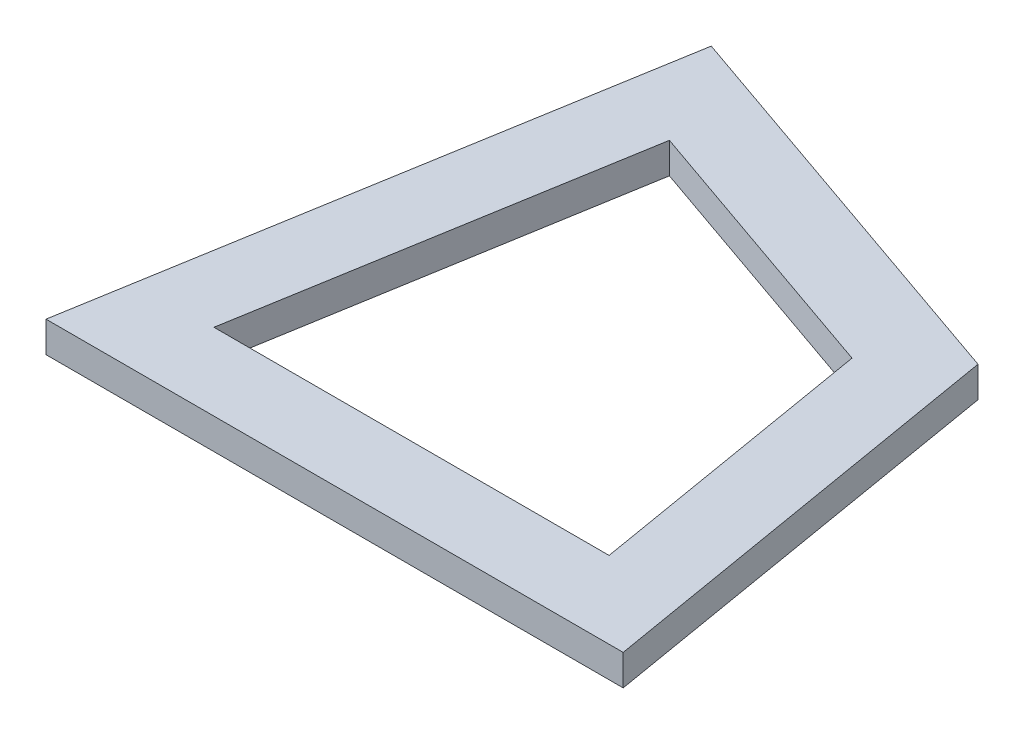
SolidWorks part; units mm, degrees
ref_plane "Front Plane" through (0, 0, 0) normal (0, 0, 1) x (1, 0, 0)
ref_plane "Top Plane" through (0, 0, 0) normal (0, 1, 0) x (1, 0, 0)
ref_plane "Right Plane" through (0, 0, 0) normal (1, 0, 0) x (0, 0, -1)
sketch "Sketch1" plane through (0, 0, 0) normal (0, 1, 0) x (1, 0, 0)
  line L0 (0, 0) -> (37.5121, 0)
  line L1 (37.5121, 0) -> (32.8236, 27.7499)
  line L2 (32.8236, 27.7499) -> (6.2494, 36.9879)
  line L3 (6.2494, 36.9879) -> (0, 0)
  line L4 (10.1942, 30.3231) -> (5.9157, 5)
  line L5 (5.9157, 5) -> (31.5965, 5)
  line L6 (31.5965, 5) -> (28.3865, 23.9989)
  line L7 (28.3865, 23.9989) -> (10.1942, 30.3231)
  point P4 (0, 0)
  point P10 (35.273, 13.2401)
  point P11 (27.7587, 61.9651)
  point P12 (35.2745, 13.2436)
  point P13 (30.6569, 10.5612)
  point P14 (35.2745, 13.2436)
  point P15 (32.8598, 27.5353)
  dimension "D1" = 37.5121
  dimension "D2" = 80.421
  dimension "D3" = 80.41
  dimension "D4" = 80.41
  dimension "D6" = 28.1432
  dimension "D7" = 28.1341
  dimension "D5" = 5
extrude "Boss-Extrude1" add sketch "Sketch1" along normal blind 2
